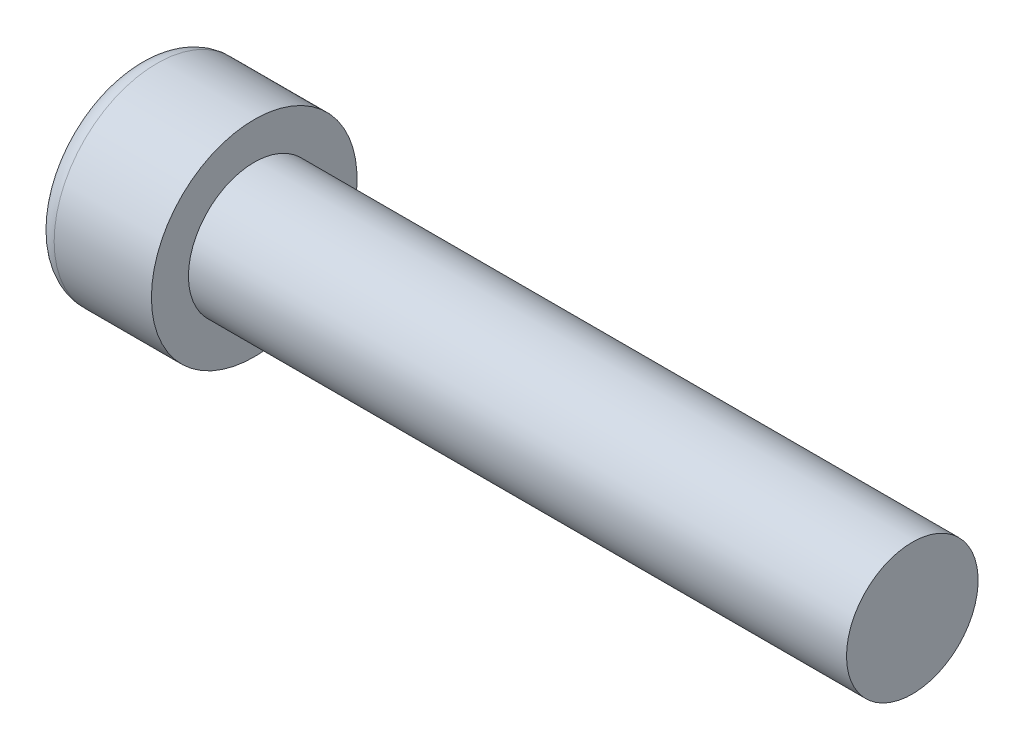
SolidWorks part; units mm, degrees
material "Plain Carbon Steel"
ref_plane "Plane1" through (0, 0, 0) normal (0, 0, 1) x (1, 0, 0)
ref_plane "Plane2" through (0, 0, 0) normal (0, 1, 0) x (1, 0, 0)
ref_plane "Plane3" through (0, 0, 0) normal (1, 0, 0) x (0, 0, -1)
sketch "BodySke" plane through (0, 0, 0) normal (0, 0, 1) x (1, 0, 0)
  line L0 (1.6, 0.8) -> (1.6, 1.25)
  line L1 (2, 6.35) -> (2, -3.175) construction
  line L2 (-25.4, 0) -> (127, 0) construction
  line L3 (9.6, 0) -> (0, 0)
  line L4 (1.6, 0.8) -> (9.6, 0.8)
  line L5 (9.6, 0.8) -> (9.6, 0)
  line L6 (0.4176, 1.25) -> (1.6, 1.25)
  line L7 (1.6, -0.8) -> (9.6, -0.8) construction
  line L8 (1.6, 6.35) -> (1.6, -3.175) construction
  arc A0 (0.192, 1.0919) -> (0, 0) centre (3.2, 0) ccw
  arc A2 (0.192, 1.0919) -> (0.4176, 1.25) centre (0.4176, 1.01) cw
  dimension "Head_crown_rad" = 3.2
  dimension "Head_fillet_rad" = 0.24
  dimension "Diameter" = 1.6
  dimension "Length" = 8
  dimension "Head_ht" = 1.6
  dimension "Head_dia" = 2.5
  dimension "Advance" = 0.4
  dimension "Thread_nom" = 8
revolve "Base-Revolve" add sketch "BodySke" angle 360 about L2
cosmetic thread "ThreadCosmetic" [suppressed] parameters "Thread_length"=7.6, "Thread_minor"=1.548
sketch "Sketch3" plane through (0, 0, 0) normal (1, 0, 0) x (0, 0, -1)
  line L0 (0.24, -0.91) -> (-0.24, -0.91)
  line L1 (0.24, -0.91) -> (0.24, 0.91)
  line L2 (-0.24, 0.91) -> (0.24, 0.91)
  line L3 (-0.24, 0.91) -> (-0.24, -0.91)
  dimension "Cross_dia" = 1.82
  dimension "D1" = 0.91
  dimension "Cross_width" = 0.48
  dimension "D2" = 0.24
ref_plane "Plane4" through (1.19, 0, 0) normal (1, 0, 0) x (0, 0, -1)
sketch "Sketch4" plane through (1.19, 0, 0) normal (1, 0, 0) x (0, 0, -1)
  line L0 (0.12, -0.12) -> (-0.12, -0.12)
  line L1 (0.12, -0.12) -> (0.12, 0.12)
  line L2 (-0.12, 0.12) -> (0.12, 0.12)
  line L3 (-0.12, 0.12) -> (-0.12, -0.12)
  dimension "D2" = 0.24
  dimension "D1" = 0.24
  dimension "D3" = 0.12
  dimension "D4" = 0.12
loft "Cut-Loft1" cut profiles "Sketch3", "Sketch4"
pattern_circular "CirPattern1" count 2 every 90 about axis through (0, 0, 0) along (1, 0, 0) of "Cut-Loft1"
sketch "ThdSchSke" plane through (0, 0, 0) normal (0, 0, 1) x (1, 0, 0)
  line L0 (2, -0.774) -> (1.9818, -0.8)
  line L1 (2, -0.774) -> (2.0182, -0.8)
  line L2 (2.0182, -0.8) -> (2.0182, -1)
  line L3 (-3.175, 0) -> (5.1513, 0) construction
  line L5 (2.0182, -1) -> (1.9818, -1)
  line L6 (1.9818, -1) -> (1.9818, -0.8)
  dimension "Diameter" = 1.6
  dimension "SideAngle" = 55
  dimension "VeeAngle" = 70
  dimension "Thread_minor" = 1.548
  dimension "Overcut" = 2
  dimension "Start" = 2
revolve "ThreadSchematic" [suppressed] cut sketch "ThdSchSke" angle 360 about L3
pattern_linear "ThdSchPat" [suppressed]
equation "\"D1@Sketch3\" = \"Cross_dia@Sketch3\" / 2"
equation "\"D2@Sketch3\" = \"Cross_width@Sketch3\" / 2"
equation "\"D1@Sketch4\" = \"Cross_width@Sketch3\" *.5"
equation "\"D2@Sketch4\" = \"D1@Sketch4\""
equation "\"D3@Sketch4\" = \"D1@Sketch4\" / 2"
equation "\"D4@Sketch4\" = \"D2@Sketch4\" / 2"
equation "\"Thread_length@ThreadCosmetic\" = ((sgn( (\"Length@BodySke\" - \"Advance@BodySke\" ) - \"Thread_nom@BodySke\" )-1)*( (\"Length@BodySke\" - \"Advance@BodySke\" ) - \"Thread_nom@BodySke\" ))/-2+ \"Thread_nom@BodySke\""
equation "\"Thread_minor@ThdSchSke\" = \"Thread_minor@ThreadCosmetic\""
equation "\"Diameter@ThdSchSke\" = \"Diameter@BodySke\""
equation "\"Overcut@ThdSchSke\" = \"Diameter@BodySke\" * 1.25"
equation "\"Start@ThdSchSke\" = \"Head_ht@BodySke\" + \"Length@BodySke\" - \"Thread_length@ThreadCosmetic\"  '---Non-countersunk---"
equation "\"Num_threads@ThdSchPat\" = int( \"Thread_length@ThreadCosmetic\" / \"Advance@BodySke\" + 0.999 )  + 1"
equation "\"Advance@ThdSchPat\" = \"Thread_length@ThreadCosmetic\" /  (\"Num_threads@ThdSchPat\" - 1) 'relax it"
